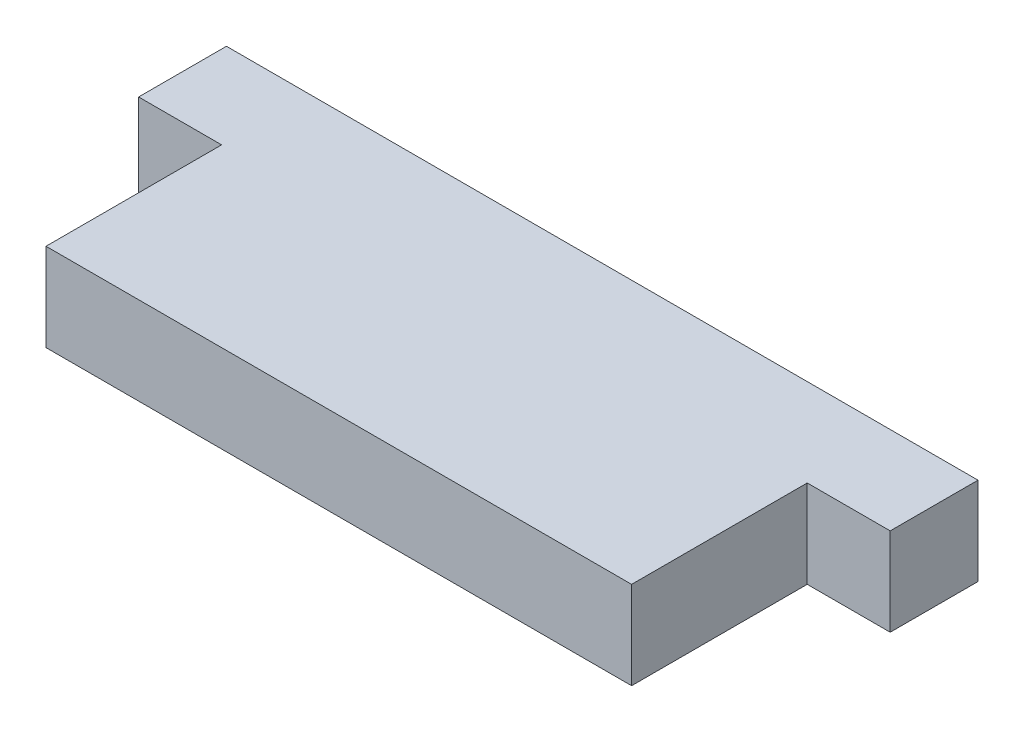
SolidWorks part; units mm, degrees
ref_plane "Front Plane" through (0, 0, 0) normal (0, 0, 1) x (1, 0, 0)
ref_plane "Top Plane" through (0, 0, 0) normal (0, 1, 0) x (1, 0, 0)
ref_plane "Right Plane" through (0, 0, 0) normal (1, 0, 0) x (0, 0, -1)
sketch "Sketch1" plane through (0, 0, 0) normal (0, 1, 0) x (1, 0, 0)
  line L0 (0, 0) -> (0, 12.7)
  line L1 (0, 0) -> (42.35, 0)
  line L3 (42.35, 0) -> (42.35, 12.7)
  line L4 (-6.0001, 19.05) -> (48.3501, 19.05)
  line L5 (-6.0001, 19.05) -> (-6.0001, 12.7)
  line L6 (48.3501, 19.05) -> (48.3501, 12.7)
  line L7 (-6.0001, 12.7) -> (0, 12.7)
  line L8 (42.35, 12.7) -> (48.3501, 12.7)
  dimension "D1" = 12.7
  dimension "D2" = 42.35
  dimension "D3" = 6.35
  dimension "D4" = 6.0001
  dimension "D5" = 6.0001
extrude "Boss-Extrude1" add sketch "Sketch1" along normal blind 6.35
equation "\"vigorwidth\"= 0.472441in"
equation "\"vigorflangewidth\"= 0.731102in"
equation "\"vigorflangelength\"= 0.131102in"
equation "\"vigorscrewsize\"= 0.066535in"
equation "\"vigorholeoffsetwid\"= 0.0646653in"
equation "\"vigorholeoffsetlen\"= 0.065551in"
equation "\"vigorflangedepth\"= 0.0901575in"
equation "\"vigordiscdepth\"= 0.0492126in"
equation "\"vigormotordepth\"= 1.12362in"
equation "\"vigortipdepth\"= 0.259055in"
equation "\"vigoraxlewidth\"= 0.173622in"
equation "\"vigorcutlen\"= 0.0480315in"
equation "\"vigoraxledepth\"= 0.159055in"
equation "\"MotorMountLegLength\"=.25in"
equation "\"GearOffset\"=.264907in"
equation "\"D4@Sketch1\" = \"TriggerRackOffset\""
equation "\"D5@Sketch1\"= \"TriggerRackOffset\""
equation "\"D2@Sketch1\" = \"CageLeftBottomEdge\" + \"CageRightBottomEdge\""
equation "\"CageLeftBottomEdge\"=21.15mm"
equation "\"CageLeftTopEdge\"=22.11mm"
equation "\"CageRightBottomEdge\"=21.20mm"
equation "\"CageRightTopEdge\"=21.63mm"
equation "\"CageHeight\"=86.04mm"
equation "\"CageLength\"=73.76mm"
equation "\"CageTopScrewClearance\"=10mm"
equation "\"CageBottomScrewClearance\"=25mm"
equation "\"CageLeftTopDepth\"= 11.65mm"
equation "\"CageLeftBottomDepth\"=10.15mm"
equation "\"CageLeftTopHeight\"=10.56175mm"
equation "\"CageLeftBottomHeight\"=16mm"
equation "\"CageRightTopDepth\"= 11.15mm"
equation "\"CageRightBottomDepth\"=10.15mm"
equation "\"CageRightTopHeight\"=9.775mm"
equation "\"CageRightBottomHeight\"=15.49mm"
equation "\"CageLeftTopChannelDepth\"=2.41908mm"
equation "\"CageLeftBottomChannelDepth\"=2.588mm"
equation "\"CageLeftChannelHeight\"=11.7mm"
equation "\"CageRightTopChannelDepth\"=2.59mm"
equation "\"CageRightBottomChannelDepth\"=2.318mm"
equation "\"CageRightChannelHeight\"=10mm"
equation "\"CageChanRelHeight\"=23.99mm"
equation "\"CageChanRelDepth\"=5.492mm"
equation "\"CageChamberRadius\"=16.261mm"
equation "\"CageScrewDiameter\"=4.8mm"
equation "\"CageSetScrewDiameter\"=3.5mm"
equation "\"CageAxleRadius\"=6.639mm"
equation "\"CageAxleKeyHeight\"=1.619mm"
equation "\"CageAxleKeyWidth\"=2.662mm"
equation "\"CageHoseWindowWidth\"=16.29mm"
equation "\"CageHoseWindowHeight\"=26.5mm"
equation "\"CageHoseWindow-Edge\"=8.89mm"
equation "\"CageScrew-VerticalEdge\"=5.0mm"
equation "\"CageScrew-HorizontalEdge\"=7.5mm"
equation "\"CageScrew-HoseCornerScrewEdge\"=4.45mm"
equation "\"CageAxle-BottomEdge\"=56.05mm"
equation "\"CageAxle-FrontEdge\"=46.03mm"
equation "\"CageBackSetScrew-Axle\"=40mm"
equation "\"CageFrontSetScrew-Axle\"=22mm"
equation "\"CageVelocityWindow-BackEdge\"=34.8mm"
equation "\"CageVelocityWindow-BottomEdge\"=27.55mm"
equation "\"CageVelocityWindowHeight\"=22.29mm"
equation "\"CageVelocityWindowWidth\"=12.61mm"
equation "\"TriggerSlot-BottomEdge\"=6.35mm"
equation "\"TriggerSlot-FrontEdge\"=15mm"
equation "\"TriggerSlotSize\"=6.7mm"
equation "\"TriggerRackOffset\"=.236224in"
equation "\"TriggerSlotSizeInt\"=.25in"
equation "\"TriggerSlotSpacing\"=.25in"
